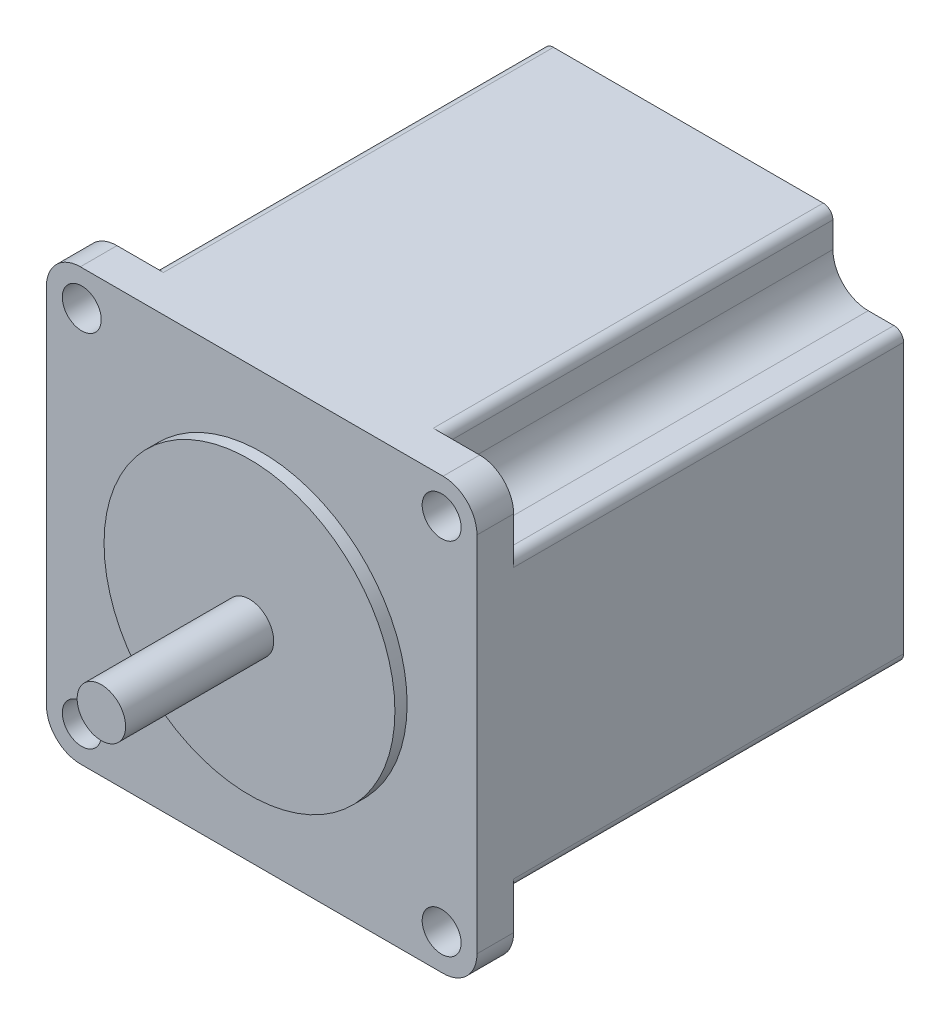
SolidWorks part; units mm, degrees
ref_plane "Front Plane" through (0, 0, 0) normal (0, 0, 1) x (1, 0, 0)
ref_plane "Top Plane" through (0, 0, 0) normal (0, 1, 0) x (1, 0, 0)
ref_plane "Right Plane" through (0, 0, 0) normal (1, 0, 0) x (0, 0, -1)
sketch "Sketch1" plane through (0, 0, 0) normal (0, 0, 1) x (1, 0, 0)
  line L0 (0, -28.2) -> (0, 28.2) construction
  line L1 (-23.755, -28.2) -> (23.755, -28.2)
  line L2 (-28.2, -23.755) -> (-28.2, 23.755)
  line L3 (-23.755, 28.2) -> (23.755, 28.2)
  line L4 (28.2, -23.755) -> (28.2, 23.755)
  line L5 (-23.57, -23.57) -> (23.57, 23.57) construction
  circle A0 centre (-23.57, 23.57) radius 2.55
  circle A1 centre (23.57, 23.57) radius 2.55
  circle A2 centre (23.57, -23.57) radius 2.55
  circle A3 centre (-23.57, -23.57) radius 2.55
  arc A4 (-23.755, 28.2) -> (-28.2, 23.755) centre (-23.755, 23.755) ccw
  arc A5 (-28.2, -23.755) -> (-23.755, -28.2) centre (-23.755, -23.755) ccw
  arc A6 (23.755, -28.2) -> (28.2, -23.755) centre (23.755, -23.755) ccw
  arc A7 (28.2, 23.755) -> (23.755, 28.2) centre (23.755, 23.755) ccw
  point P17 (-28.2, 28.2)
  point P20 (-28.2, -28.2)
  point P25 (28.2, 28.2)
  dimension "D3" = 5.1
  dimension "D4" = 5.1
  dimension "D5" = 5.1
  dimension "D6" = 5.1
  dimension "D9" = 4.445
  dimension "D1" = 56.4
  dimension "D2" = 56.4
  dimension "D7" = 47.14
  dimension "D8" = 47.14
extrude "Boss-Extrude1" add sketch "Sketch1" along normal blind 4.8
sketch "Sketch2" plane through (0, 0, 0) normal (0, 0, -1) x (-1, 0, 0)
  line L0 (23.57, -18.94) -> (26.93, -18.94)
  line L1 (-28.2, 28.2) -> (28.2, 28.2) construction
  line L2 (-28.2, 28.2) -> (-28.2, -28.2) construction
  line L3 (-28.2, -28.2) -> (28.2, -28.2) construction
  line L4 (28.2, 28.2) -> (28.2, -28.2) construction
  line L5 (18.94, -23.57) -> (18.94, -26.93)
  line L6 (-18.9363, -23.57) -> (-18.9363, -26.93)
  line L7 (-23.57, -18.9363) -> (-26.93, -18.9363)
  line L8 (-18.94, 23.57) -> (-18.94, 26.93)
  line L9 (-23.57, 18.94) -> (-26.93, 18.94)
  line L10 (23.57, 18.9363) -> (26.93, 18.9363)
  line L11 (18.9363, 23.57) -> (18.9363, 26.93)
  line L12 (23.755, -28.2) -> (-23.755, -28.2) construction
  line L13 (28.2, 23.755) -> (28.2, -23.755) construction
  line L14 (-28.2, -23.755) -> (-28.2, 23.755) construction
  line L15 (-17.67, 28.2) -> (17.6663, 28.2)
  line L16 (28.2, 17.6663) -> (28.2, -17.67)
  line L17 (17.67, -28.2) -> (-17.6663, -28.2)
  line L18 (-28.2, -17.6663) -> (-28.2, 17.67)
  arc A0 (-18.94, 23.57) -> (-23.57, 18.94) centre (-23.57, 23.57) ccw construction
  arc A1 (23.57, -18.94) -> (18.94, -23.57) centre (23.57, -23.57) ccw
  arc A2 (-23.57, -18.9363) -> (-18.9363, -23.57) centre (-23.57, -23.57) ccw construction
  arc A3 (18.9363, 23.57) -> (23.57, 18.9363) centre (23.57, 23.57) ccw
  arc A4 (-18.9363, -23.57) -> (-23.57, -18.9363) centre (-23.57, -23.57) ccw
  arc A5 (18.94, -23.57) -> (23.57, -18.94) centre (23.57, -23.57) ccw construction
  arc A6 (23.57, 18.9363) -> (18.9363, 23.57) centre (23.57, 23.57) ccw construction
  arc A7 (-23.57, 18.94) -> (-18.94, 23.57) centre (-23.57, 23.57) ccw
  arc A8 (-26.93, 18.94) -> (-28.2, 17.67) centre (-26.93, 17.67) ccw
  arc A9 (-28.2, -17.6663) -> (-26.93, -18.9363) centre (-26.93, -17.6663) ccw
  arc A10 (-18.9363, -26.93) -> (-17.6663, -28.2) centre (-17.6663, -26.93) ccw
  arc A11 (17.67, -28.2) -> (18.94, -26.93) centre (17.67, -26.93) ccw
  arc A12 (26.93, -18.94) -> (28.2, -17.67) centre (26.93, -17.67) ccw
  arc A13 (28.2, 17.6663) -> (26.93, 18.9363) centre (26.93, 17.6663) ccw
  arc A14 (18.9363, 26.93) -> (17.6663, 28.2) centre (17.6663, 26.93) ccw
  arc A15 (-18.94, 26.93) -> (-17.67, 28.2) centre (-17.67, 26.93) cw
  point P20 (-28.2, 18.94)
  point P30 (-28.2, -18.9363)
  point P44 (-18.9363, -28.2)
  point P47 (18.94, -28.2)
  point P50 (28.2, -18.94)
  point P53 (28.2, 18.9363)
  point P56 (18.9363, 28.2)
  point P59 (-18.94, 28.2)
  dimension "D1" = 1.27
extrude "Boss-Extrude2" add sketch "Sketch2" along normal offset from surface (51.08 mm away) 55.88 up to face at (26.12, -23.57, 4.8)
sketch "Sketch3" plane through (0, 0, 4.8) normal (0, 0, 1) x (1, 0, 0)
  circle A0 centre (0, 0) radius 19.05
  dimension "D1" = 38.1
extrude "Boss-Extrude3" add sketch "Sketch3" along normal blind 1.6
sketch "Sketch4" plane through (0, 0, 6.4) normal (0, 0, 1) x (1, 0, 0)
  circle A0 centre (0, 0) radius 3.175
  dimension "D1" = 6.35
extrude "Boss-Extrude8" add sketch "Sketch4" along normal blind 19.4
sketch "Mounting Holes" plane through (0, 0, 4.8) normal (0, 0, 1) x (1, 0, 0)
  line L8 (-28.2, 23.755) -> (-28.2, -23.755)
  line L9 (-23.755, -28.2) -> (23.755, -28.2)
  line L10 (28.2, -23.755) -> (28.2, 23.755)
  line L11 (23.755, 28.2) -> (-23.755, 28.2)
  line L12 (-28.2, 23.755) -> (-28.2, -23.755)
  line L13 (-23.755, -28.2) -> (23.755, -28.2)
  line L14 (28.2, -23.755) -> (28.2, 23.755)
  line L15 (23.755, 28.2) -> (-23.755, 28.2)
  circle A0 centre (0, 0) radius 19.05
  circle A1 centre (-23.57, 23.57) radius 2.55
  circle A2 centre (23.57, 23.57) radius 2.55
  circle A3 centre (23.57, -23.57) radius 2.55
  circle A4 centre (-23.57, -23.57) radius 2.55
  arc A8 (-23.755, 28.2) -> (-28.2, 23.755) centre (-23.755, 23.755) ccw
  arc A9 (-28.2, -23.755) -> (-23.755, -28.2) centre (-23.755, -23.755) ccw
  arc A10 (23.755, -28.2) -> (28.2, -23.755) centre (23.755, -23.755) ccw
  arc A11 (28.2, 23.755) -> (23.755, 28.2) centre (23.755, 23.755) ccw
  arc A12 (-23.755, 28.2) -> (-28.2, 23.755) centre (-23.755, 23.755) ccw
  arc A13 (-28.2, -23.755) -> (-23.755, -28.2) centre (-23.755, -23.755) ccw
  arc A14 (23.755, -28.2) -> (28.2, -23.755) centre (23.755, -23.755) ccw
  arc A15 (28.2, 23.755) -> (23.755, 28.2) centre (23.755, 23.755) ccw
  dimension "D1" = 0
